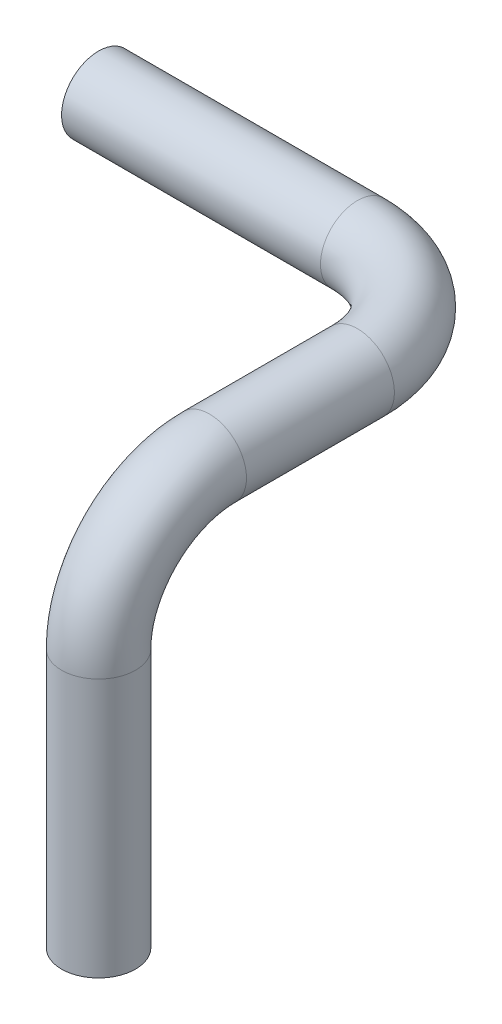
SolidWorks part; units mm, degrees
ref_plane "Front Plane" through (0, 0, 0) normal (0, 0, 1) x (1, 0, 0)
ref_plane "Top Plane" through (0, 0, 0) normal (0, 1, 0) x (1, 0, 0)
ref_plane "Right Plane" through (0, 0, 0) normal (1, 0, 0) x (0, 0, -1)
sketch3d "3DSketch1"
  line L0 (0, 254, 0) -> (177.8, 254, 0)
  line L1 (254, 254, 76.2) -> (254, 254, 177.8)
  line L2 (254, 177.8, 254) -> (254, 0, 254)
  arc A0 (177.8, 254, 0) -> (254, 254, 76.2) centre (177.8, 254, 76.2) ccw
  arc A1 (254, 254, 177.8) -> (254, 177.8, 254) centre (254, 177.8, 177.8) ccw
  point P0 (0, 254, 0)
  point P5 (0, 0, 0)
  point P6 (0, 0, 0)
  point P7 (0, 0, 0)
  point P10 (254, 254, 0)
  point P11 (177.8, 177.8, 76.2)
  point P14 (254, 254, 254)
  point P15 (330.2, 177.8, 177.8)
  dimension "D1" = 76.2
sweep "Sweep1" add path "3DSketch1" circular profile diameter 50.8 parameters "D3"=50.8
shell "Shell1" thickness 2.54
